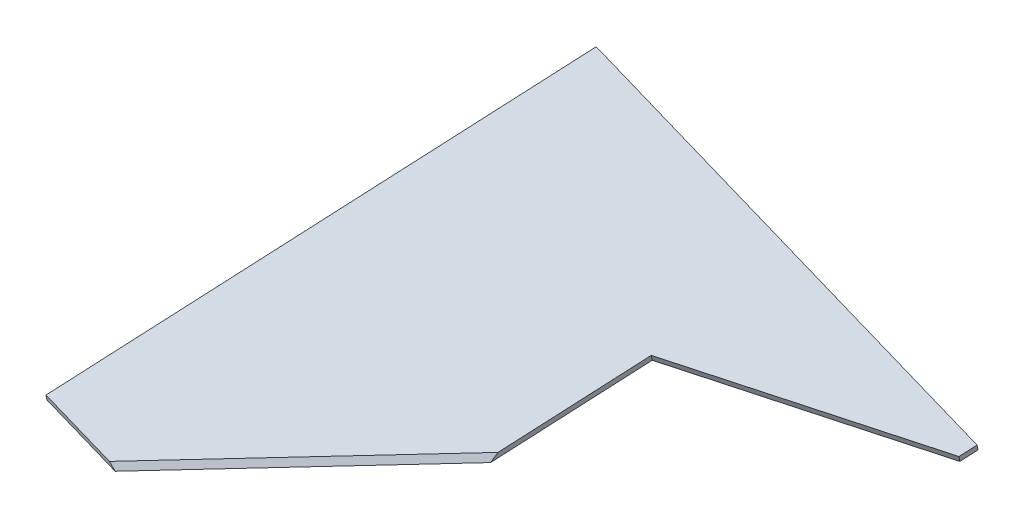
SolidWorks part; units mm, degrees
ref_plane "Front Plane" through (0, 0, 0) normal (0, 0, 1) x (1, 0, 0)
ref_plane "Top Plane" through (0, 0, 0) normal (0, 1, 0) x (1, 0, 0)
ref_plane "Right Plane" through (0, 0, 0) normal (1, 0, 0) x (0, 0, -1)
sketch "Sketch1" plane through (40.619, 405.7175, 71.3913) normal (-0.119, -0.9518, -0.2826) x (0.9357, -0.2027, 0.2888)
  line L8 (-9.0936, 199.4964) -> (122.6459, 181.2284)
  line L9 (-9.0936, 199.4964) -> (-43.9027, -51.5299)
  line L10 (122.6459, 181.2284) -> (87.8367, -69.7979)
  line L11 (-43.9027, -51.5299) -> (87.8367, -69.7979)
  line L13 (84.842, -91.394) -> (113.6696, 116.4958) construction
  line L14 (-9.0936, 199.4964) -> (-6.122, 199.0843) construction
  line L15 (-43.9027, -51.5299) -> (-9.0936, 199.4964) construction
  line L16 (-43.9027, -51.5299) -> (-40.9312, -51.942) construction
extrude "Boss-Extrude1" add sketch "Sketch1" against normal blind 3
sketch "Sketch3" plane through (184.7627, 119.8973, 240.0695) normal (0.5671, 0.368, 0.7369) x (0.5168, 0.5377, -0.6662)
  line L4 (970.9378, -219.8867) -> (970.9378, 845.2452)
  line L5 (970.9378, -219.8867) -> (-1124.2865, -289.5005)
  line L6 (970.9378, 845.2452) -> (-1124.2865, 775.6314)
  line L7 (-1124.2865, -289.5005) -> (-1124.2865, 775.6314)
extrude "Cut-Extrude2" cut sketch "Sketch3" along normal blind 80
sketch "Sketch4" plane through (48.9104, 391.3748, 116.2066) normal (-0.119, -0.9518, -0.2826) x (0.9929, -0.1167, -0.0249)
  line L0 (83.714, -16.7502) -> (96.9933, -84.3458)
  line L2 (96.9933, -84.3458) -> (209.4439, -62.2545)
  line L3 (209.4439, -62.2545) -> (207.8348, -54.0636)
  line L5 (207.8348, -54.0636) -> (83.714, -16.7502)
  line L6 (96.9933, -84.3458) -> (69.3656, 56.2868) construction
  line L7 (101.1962, -105.7396) -> (60.7381, 100.2029) construction
  line L10 (192.7528, 22.7076) -> (173.9482, 118.4281) construction
extrude "Boss-Extrude2" add sketch "Sketch4" against normal blind 3
